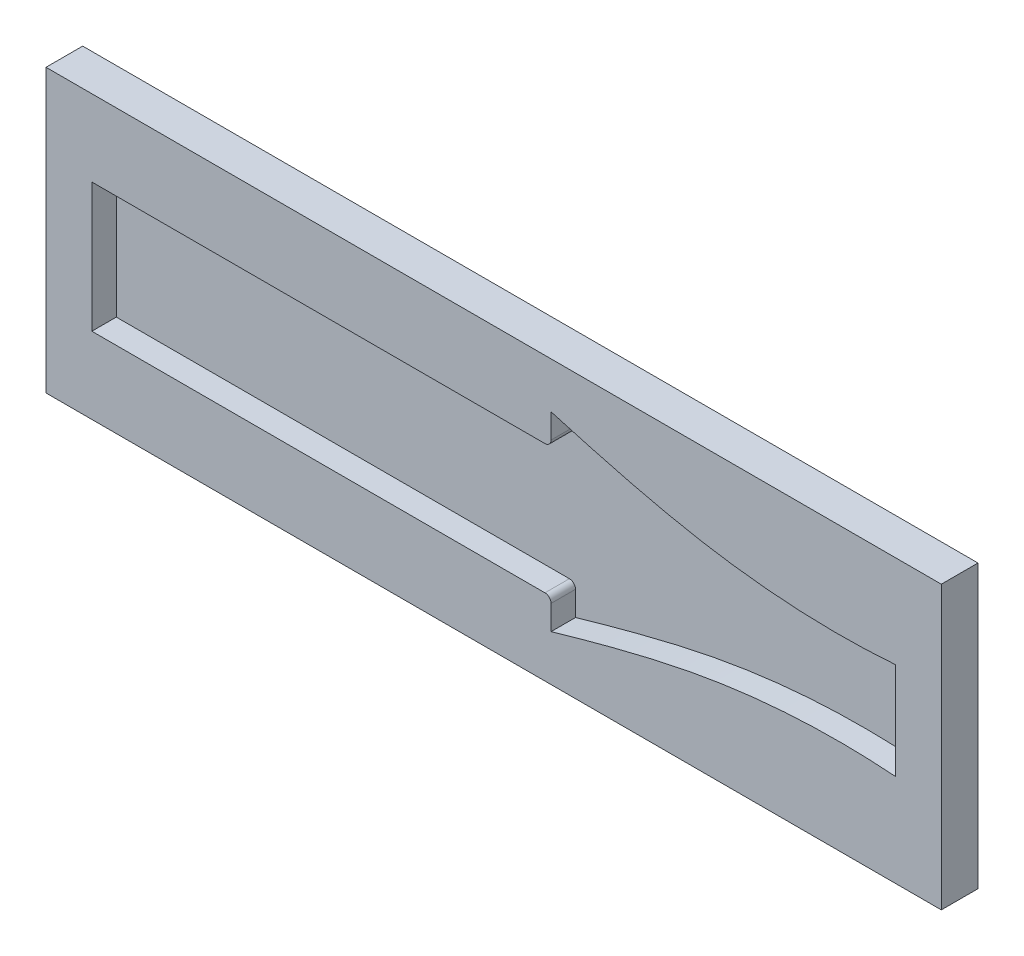
SolidWorks part; units mm, degrees
ref_plane "Front Plane" through (0, 0, 0) normal (0, 0, 1) x (1, 0, 0)
ref_plane "Top Plane" through (0, 0, 0) normal (0, 1, 0) x (1, 0, 0)
ref_plane "Right Plane" through (0, 0, 0) normal (1, 0, 0) x (0, 0, -1)
sketch "Sketch2" plane through (0, 0, 0) normal (0, 0, 1) x (1, 0, 0)
  line L0 (-34.9057, 0) -> (224.3031, 0) construction
  line L1 (224.3031, 0) -> (301.3454, 0) construction
  line L2 (183.75, 43.8118) -> (183.75, 27.5) construction
  line L3 (287.25, 7.8125) -> (287.25, -7.8125)
  line L5 (231, 15.4713) -> (156, 15.4713)
  line L8 (156, 15.4713) -> (156, -15.4713)
  line L9 (183.75, -27.5) -> (183.75, -35.6953) construction
  line L10 (231, -15.4713) -> (156, -15.4713)
  spline S0 degree 3 poles (231, 15.4713) (231.9161, 15.2083) (240.1703, 12.8537) (258.5979, 8.0187) (276.8427, 7.0195) (287.25, 7.8125) knots 0.46088 0.46088 0.46088 0.46088 0.487879 0.704009 1 1 1 1
  spline S1 degree 3 poles (231, -15.4713) (231.9161, -15.2083) (240.1703, -12.8537) (258.5979, -8.0187) (276.8427, -7.0195) (287.25, -7.8125) knots 0.46088 0.46088 0.46088 0.46088 0.487879 0.704009 1 1 1 1
  point P3 (183.75, 0)
  point P5 (196.25, 0)
  point P6 (208.75, 0)
  point P7 (221.75, 0)
  point P8 (233.75, 0)
  point P9 (246.25, 0)
  point P10 (249.75, 0)
  point P11 (256, 0)
  point P12 (262.25, 0)
  point P13 (268.5, 0)
  point P14 (274.75, 0)
  point P15 (281, 0)
  point P16 (287.25, 0)
  point P19 (196.25, 24.375)
  point P20 (183.75, 27.5)
  point P21 (208.75, 21.875)
  point P22 (221.75, 18.3125)
  point P23 (233.75, 14.6875)
  point P24 (246.25, 11.875)
  point P25 (249.75, 11.25)
  point P26 (256, 9.375)
  point P27 (262.25, 8.125)
  point P28 (268.5, 7.5)
  point P29 (274.75, 7.5)
  point P30 (281, 7.5)
  point P31 (287.25, 7.8125)
  point P46 (231, 15.4713)
  point P47 (231, 0)
  point P48 (231, -15.4713)
  point P55 (156, 0)
sketch "Sketch3" plane through (0, 0, 0) normal (0, 0, 1) x (1, 0, 0)
  line L0 (0, 0) -> (369.6074, 0) construction
  line L2 (148.4, 23.0713) -> (294.85, 23.0713)
  line L3 (148.4, 23.0713) -> (148.4, -23.0713)
  line L4 (148.4, -23.0713) -> (294.85, -23.0713)
  line L5 (294.85, 23.0713) -> (294.85, -23.0713)
  line L8 (231.0141, 15.5713) -> (155.9, 15.5713)
  line L9 (155.9, 15.5713) -> (155.9, -15.5713)
  line L10 (155.9, -15.5713) -> (231.0141, -15.5713)
  line L11 (287.35, -7.9204) -> (287.35, 7.9204)
  line L12 (231.0141, 15.5713) -> (155.9, 15.5713)
  line L13 (155.9, 15.5713) -> (155.9, -15.5713)
  line L14 (155.9, -15.5713) -> (231.0141, -15.5713)
  line L15 (287.35, -7.9204) -> (287.35, 7.9204)
  spline S4 degree 3 poles (-945.5227, 2724.6611) (-0.1248, -219.1596) (103.6898, -46.3607) (247.1619, -11.267) (249.4894, -10.738) (254.1656, -9.7872) (256.5148, -9.3668) (263.6013, -8.3014) (268.3381, -7.8488) (275.4561, -7.5683) (277.8312, -7.5414) (590.9306, -13.0859) (947.0432, -1233.8364) (1109.9232, 2718.8129) knots -7.356317 -7.356317 -7.356317 -7.356317 0.25 0.25 0.375 0.375 0.5 0.5 0.75 0.75 0.875 0.875 17.21001 17.21001 17.21001 17.21001 only from (231.0141, -15.5713) to (287.35, -7.9204)
  spline S5 degree 3 poles (1169.0793, -2744.3491) (823.663, 1005.2705) (560.4996, 12.5354) (277.8206, 7.5413) (275.4362, 7.5685) (268.2793, 7.8524) (263.5326, 8.3094) (256.451, 9.3776) (254.1043, 9.7988) (249.438, 10.7493) (247.1174, 11.2775) (103.4424, 46.4469) (-4.8944, 220.6475) (-859.5588, -2759.7607) knots -14.576282 -14.576282 -14.576282 -14.576282 0.125 0.125 0.25 0.25 0.5 0.5 0.625 0.625 0.75 0.75 8.393847 8.393847 8.393847 8.393847 only from (287.35, 7.9204) to (231.0141, 15.5713)
  spline S6 degree 3 poles (231.0141, -15.5713) (235.6039, -14.2534) (240.2029, -12.9692) (247.1619, -11.267) (249.4894, -10.738) (254.1656, -9.7872) (256.5148, -9.3668) (263.6013, -8.3014) (268.3381, -7.8488) (275.4561, -7.5683) (277.8312, -7.5414) (282.5867, -7.6256) (284.9671, -7.7388) (287.35, -7.9204) knots 0 0 0 0 0.25 0.25 0.375 0.375 0.5 0.5 0.75 0.75 0.875 0.875 1 1 1 1
  spline S7 degree 3 poles (287.35, 7.9204) (284.9692, 7.739) (282.5871, 7.6255) (277.8206, 7.5413) (275.4362, 7.5685) (268.2793, 7.8524) (263.5326, 8.3094) (256.451, 9.3776) (254.1043, 9.7988) (249.438, 10.7493) (247.1174, 11.2775) (240.1822, 12.9751) (235.5941, 14.2562) (231.0141, 15.5713) knots 0 0 0 0 0.125 0.125 0.25 0.25 0.5 0.5 0.625 0.625 0.75 0.75 1 1 1 1
  point P7 (287.35, 0)
  dimension "D2" = 7.5
  dimension "D3" = 7.5
  dimension "D4" = 7.5
  dimension "D5" = 7.5
  dimension "D1" = 0.1
sketch "Sketch4" plane through (0, 0, 0) normal (0, 0, 1) x (1, 0, 0)
extrude "Boss-Extrude1" add sketch "Sketch3" along normal blind 10
sketch "Sketch5" plane through (0, 0, 0) normal (0, 0, 1) x (1, 0, 0)
  line L1 (148.4, 23.0713) -> (294.85, 23.0713)
  line L2 (148.4, 23.0713) -> (148.4, -23.0713)
  line L3 (148.4, -23.0713) -> (294.85, -23.0713)
  line L4 (294.85, 23.0713) -> (294.85, -23.0713)
extrude "Boss-Extrude2" add sketch "Sketch5" along normal blind 6
sketch "Sketch6" plane through (0, 0, 6) normal (0, 0, 1) x (1, 0, 0)
  line L0 (155.9, 15.5713) -> (155.9, -15.5713) construction
  line L1 (231.0141, 15.5713) -> (155.9, 15.5713)
  line L2 (231.0141, 15.5713) -> (231.0141, 11.5713)
  line L3 (230.0141, 10.5713) -> (155.9, 10.5713)
  line L4 (155.9, 15.5713) -> (155.9, 10.5713)
  line L6 (231.0141, -15.5713) -> (155.9, -15.5713)
  line L7 (231.0141, -15.5713) -> (231.0141, -11.5713)
  line L8 (230.0141, -10.5713) -> (155.9, -10.5713)
  line L9 (155.9, -15.5713) -> (155.9, -10.5713)
  arc A0 (231.0141, -11.5713) -> (230.0141, -10.5713) centre (230.0141, -11.5713) ccw
  arc A1 (231.0141, 11.5713) -> (230.0141, 10.5713) centre (230.0141, 11.5713) cw
  dimension "D1" = 1
extrude "Boss-Extrude3" add sketch "Sketch6" along normal blind 4
ref_plane "Plane1" through (0, 0, 4) normal (0, 0, 1) x (1, 0, 0)
other "SurfaceCut2"
